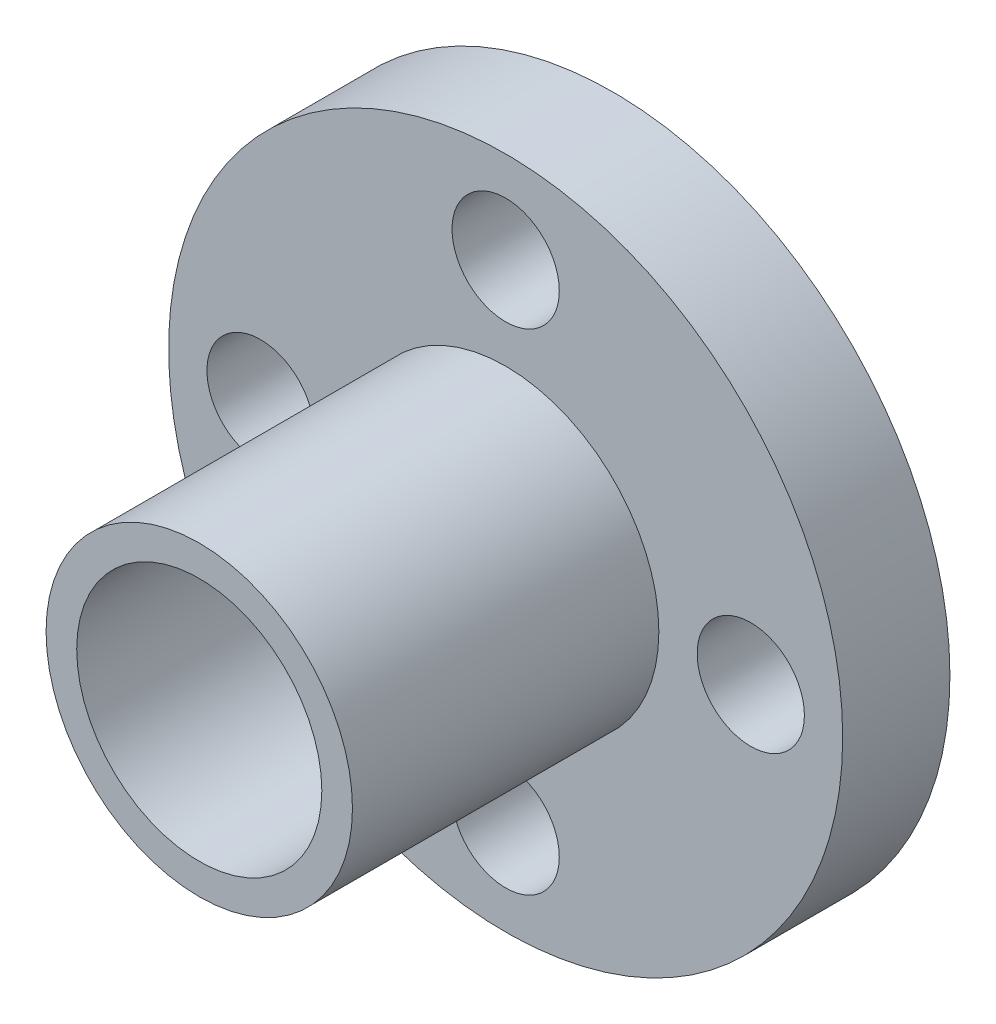
SolidWorks part; units mm, degrees
ref_plane "Front Plane" through (0, 0, 0) normal (0, 0, 1) x (1, 0, 0)
ref_plane "Top Plane" through (0, 0, 0) normal (0, 1, 0) x (1, 0, 0)
ref_plane "Right Plane" through (0, 0, 0) normal (1, 0, 0) x (0, 0, -1)
sketch "Sketch1" plane through (0, 0, 0) normal (0, 0, 1) x (1, 0, 0)
  circle A0 centre (0, 0) radius 5
  dimension "D1" = 10
extrude "Boss-Extrude1" add sketch "Sketch1" along normal blind 1.5
sketch "Sketch2" plane through (0, 0, 1.5) normal (0, 0, 1) x (1, 0, 0)
  circle A0 centre (0, 0) radius 11
  dimension "D1" = 22
extrude "Boss-Extrude2" add sketch "Sketch2" along normal blind 3.5
sketch "Sketch3" plane through (0, 0, 5) normal (0, 0, 1) x (1, 0, 0)
  circle A0 centre (0, 0) radius 5
  dimension "D1" = 10
extrude "Boss-Extrude3" add sketch "Sketch3" along normal blind 10
sketch "Sketch4" plane through (0, 0, 5) normal (0, 0, 1) x (1, 0, 0)
  circle A0 centre (0, 8) radius 1.75
  circle A1 centre (0, -8) radius 1.75
  circle A2 centre (8, 0) radius 1.75
  circle A3 centre (-8, 0) radius 1.75
  dimension "D1" = 3.5
  dimension "D2" = 3.5
  dimension "D3" = 3.5
  dimension "D4" = 3.5
  dimension "D5" = 8
  dimension "D6" = 8
  dimension "D7" = 8
  dimension "D8" = 8
extrude "Cut-Extrude1" cut sketch "Sketch4" against normal blind 4
sketch "Sketch5" plane through (0, 0, 15) normal (0, 0, 1) x (1, 0, 0)
  circle A0 centre (0, 0) radius 4
  dimension "D1" = 8
extrude "Cut-Extrude2" cut sketch "Sketch5" against normal blind 15
